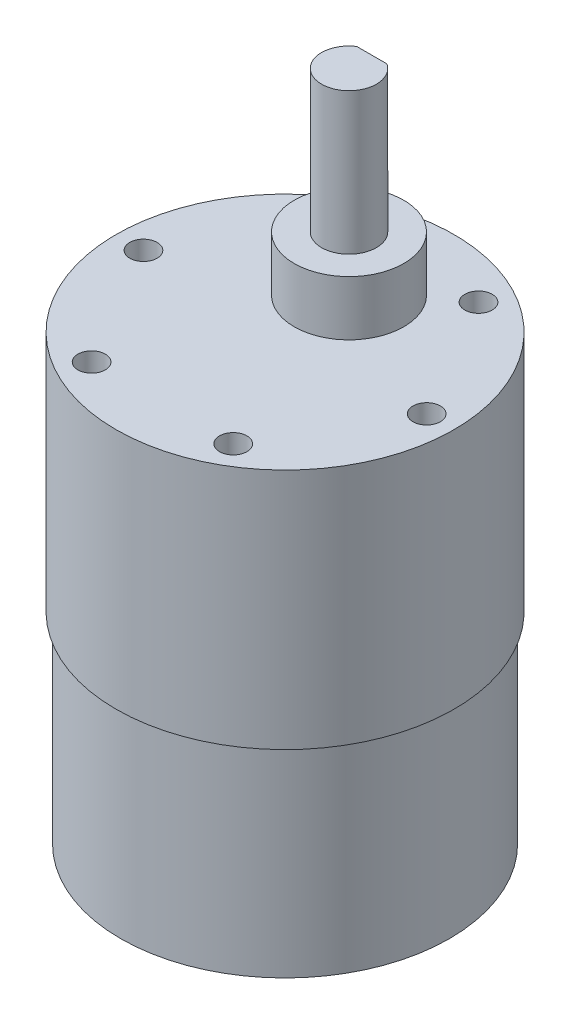
SolidWorks part; units mm, degrees
ref_plane "Front Plane" through (0, 0, 0) normal (0, 0, 1) x (1, 0, 0)
ref_plane "Top Plane" through (0, 0, 0) normal (0, 1, 0) x (1, 0, 0)
ref_plane "Right Plane" through (0, 0, 0) normal (1, 0, 0) x (0, 0, -1)
sketch "Sketch2" plane through (0, 0, 0) normal (0, 1, 0) x (1, 0, 0)
  circle A0 centre (0, 0) radius 18
  dimension "D1" = 36
extrude "Boss-Extrude1" add sketch "Sketch2" along normal blind 22
sketch "Sketch3" plane through (0, 22, 0) normal (0, 1, 0) x (1, 0, 0)
  circle A0 centre (0, 0) radius 18.5
  dimension "D1" = 37
extrude "Boss-Extrude2" add sketch "Sketch3" along normal blind 26.5
sketch "Sketch4" plane through (0, 48.5, 0) normal (0, 1, 0) x (1, 0, 0)
  circle A0 centre (-15.5, 0) radius 1.5
  dimension "D1" = 3
  dimension "D2" = 15.5
extrude "Cut-Extrude1" cut sketch "Sketch4" against normal blind 6
pattern_circular "CirPattern1" count 6 over 360 about axis through (0, 0, 0) along (0, 1, 0) of "Cut-Extrude1"
sketch "Sketch5" plane through (0, 48.5, 0) normal (0, 1, 0) x (1, 0, 0)
  line L0 (0, 18.5) -> (0, -18.5) construction
  circle A0 centre (0, 0) radius 18.5 construction
  circle A1 centre (0, 7) radius 6
  dimension "D1" = 12
  dimension "D2" = 7
extrude "Boss-Extrude3" add sketch "Sketch5" along normal blind 6
sketch "Sketch6" plane through (0, 54.5, 0) normal (0, 1, 0) x (1, 0, 0)
  circle A0 centre (0, 7) radius 3
  dimension "D1" = 6
extrude "Boss-Extrude4" add sketch "Sketch6" along normal blind 15.5
sketch "Sketch7" plane through (0, 70, 0) normal (0, 1, 0) x (1, 0, 0)
  line L0 (-1.6583, 9.5) -> (1.6583, 9.5)
  line L1 (0, 10) -> (0, 4) construction
  circle A0 centre (0, 7) radius 3 construction
  circle A1 centre (0, 7) radius 3 construction
  point P9 (0, 7)
  dimension "D1" = 2.5
  dimension "D2" = 3.3166
  dimension "D3" = 1.6583
extrude "Cut-Extrude2" cut sketch "Sketch7" against normal blind 12 and the other way through all
